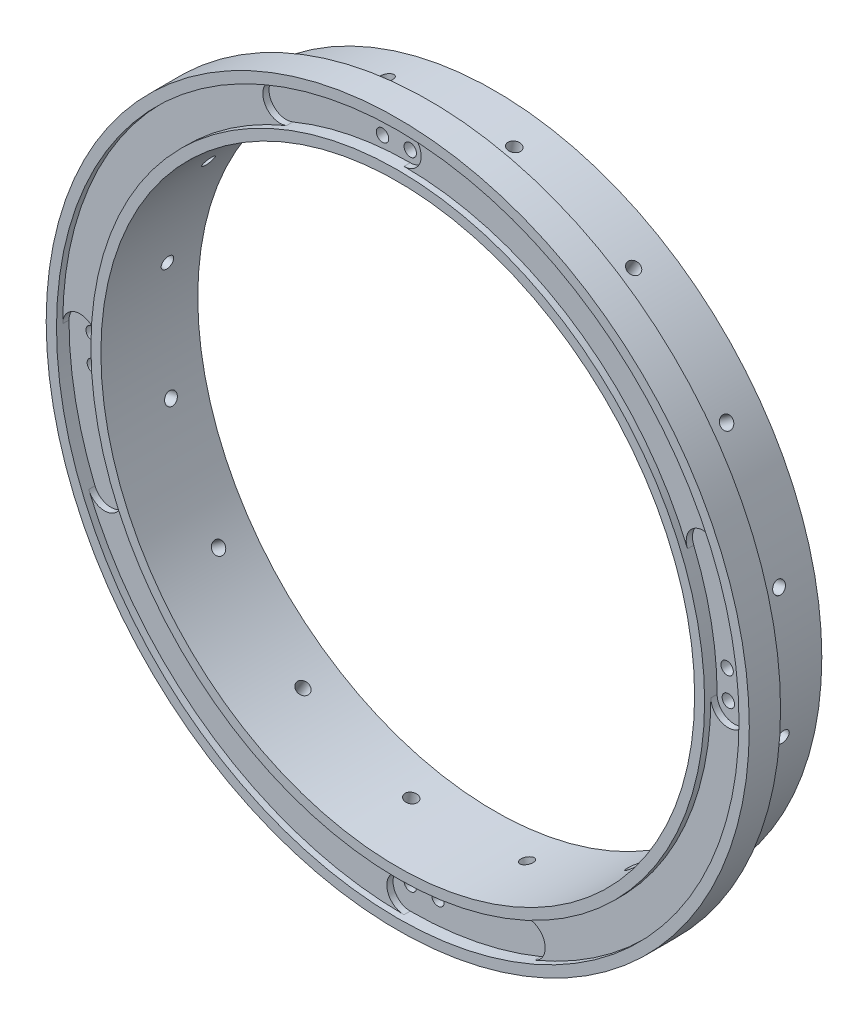
SolidWorks part; units mm, degrees
ref_plane "Front Plane" through (0, 0, 0) normal (0, 0, 1) x (1, 0, 0)
ref_plane "Top Plane" through (0, 0, 0) normal (0, 1, 0) x (1, 0, 0)
ref_plane "Right Plane" through (0, 0, 0) normal (1, 0, 0) x (0, 0, -1)
sketch "Sketch1" plane through (0, 0, 0) normal (0, 0, 1) x (1, 0, 0)
  circle A0 centre (0, 0) radius 71.4375
  dimension "D1" = 142.875
extrude "Extrude1" add sketch "Sketch1" along normal blind 19.685
sketch "Sketch2" plane through (0, 0, 19.685) normal (0, 0, 1) x (1, 0, 0)
  circle A0 centre (0, 0) radius 60.325
  dimension "D1" = 120.65
extrude "Extrude2" cut sketch "Sketch2" against normal through all
sketch "Sketch3" plane through (0, 0, 0) normal (0, 0, -1) x (-1, 0, 0)
  circle A0 centre (0, 0) radius 66.4845
  dimension "D1" = 132.969
extrude "Extrude3" cut sketch "Sketch3" against normal blind 13.335 flip side to cut
sketch "Sketch4" plane through (0, 0, 19.685) normal (0, 0, 1) x (1, 0, 0)
  circle A0 centre (0, 0) radius 62.357
  circle A1 centre (0, 0) radius 69.342
  dimension "D1" = 124.714
  dimension "D2" = 138.684
extrude "Extrude4" cut sketch "Sketch4" against normal blind 1.27
sketch "Sketch5" plane through (0, 0, 18.415) normal (0, 0, 1) x (1, 0, 0)
  line L0 (0, 0) -> (0, 69.342) construction
  line L1 (0, 69.342) -> (0, -69.342) construction
  line L2 (0, 0) -> (62.357, 0) construction
  line L3 (0, -69.342) -> (0, 0) construction
  line L4 (0, 0) -> (69.342, 0) construction
  line L5 (69.342, 0) -> (-69.342, 0) construction
  circle A0 centre (0, 0) radius 62.357 construction
  circle A2 centre (0, 0) radius 69.342 construction
sketch "Sketch7" plane through (0, 0, 18.415) normal (0, 0, 1) x (1, 0, 0)
  line L0 (69.342, 0) -> (-69.342, 0) construction
  line L1 (0, 0) -> (0, 69.342) construction
  line L2 (0, 69.342) -> (0, 62.357) construction
  line L3 (-26.536, 64.0637) -> (-23.863, 57.6104) construction
  arc A0 (0, 69.342) -> (-26.536, 64.0637) centre (0, 0) ccw
  arc A1 (0, 62.357) -> (-23.863, 57.6104) centre (0, 0) ccw
  circle A2 centre (0, 0) radius 62.357 construction
  arc A3 (-26.536, 64.0637) -> (-23.863, 57.6104) centre (-25.1995, 60.837) ccw
  arc A4 (0, 69.342) -> (0, 62.357) centre (0, 65.8495) cw
extrude "Extrude6" cut sketch "Sketch7" against normal blind 1.27 and the other way through all
pattern_circular "CirPattern1" count 4 over 360 about axis through (0, 0, 0) along (0, 0, 1) of "Extrude6"
sketch "Sketch8" plane through (0, 0, 17.145) normal (0, 0, 1) x (1, 0, 0)
  circle A0 centre (0, 0) radius 64.6327
  arc A1 (0, 64.6327) -> (-5.6331, 64.3868) centre (0, 0) ccw
hole_wizard "#39 (0.0995) Diameter Hole1" positions "3DSketch1" profile "Sketch9" hole size "#39" standard "Ansi Inch" end condition through all
sketch3d "3DSketch1"
  point P0 (0, 64.6327, 17.145)
  point P3 (-5.6331, 64.3868, 17.145)
sketch "Sketch9" plane through (0, 64.6327, 17.145) normal (1, 0, 0) x (0, -1, 0)
  line L0 (0, 0) -> (0, 17.145)
  line L1 (0, 17.145) -> (1.2636, 17.145)
  line L2 (1.2636, 17.145) -> (1.2636, 0)
  line L5 (1.2636, 0) -> (0, 0)
  line L11 (0, -6.35) -> (0, 107.95) construction
  dimension "Thru Hole Dia." = 2.5273
  dimension "Thru Hole Depth" = 17.145
pattern_circular "CirPattern2" count 4 over 360 about axis through (0, 0, 0) along (0, 0, 1) of "#39 (0.0995) Diameter Hole1"
ref_plane "Plane1" through (0, 0, 6.985) normal (0, 0, -1) x (-1, 0, 0)
sketch "Sketch15" plane through (0, 0, 6.985) normal (0, 0, -1) x (-1, 0, 0)
  line L0 (0, 0) -> (-66.4845, 0) construction
  line L1 (-2.314, 46.2834) -> (-2.314, 63.5529) construction
  line L2 (0, 0) -> (-69.342, 0) construction
  line L3 (0, 0) -> (-64.7805, 14.9558) construction
  circle A0 centre (0, 0) radius 66.4845 construction
ref_plane "Plane3" through (64.7805, 14.9558, 6.985) normal (0.9744, 0.225, 0) x (0, 0, -1)
hole_wizard "#39 (0.0995) Diameter Hole5" positions "Sketch17" profile "Sketch16" hole size "#39" standard "Ansi Inch"
sketch "Sketch17" plane through (64.7805, 14.9558, 6.985) normal (0.9744, 0.225, 0) x (0, 0, -1)
  point P1 (0, 0)
sketch "Sketch16" plane through (64.7805, 14.9558, 6.985) normal (0, 0, 1) x (-0.225, 0.9744, 0)
  line L0 (0, 0) -> (0, 13.4593)
  line L1 (0, 13.4593) -> (1.2636, 12.7)
  line L2 (1.2636, 12.7) -> (1.2636, 0)
  line L5 (1.2636, 0) -> (0, 0)
  line L10 (0, 13.4593) -> (-1.2636, 12.7) construction
  line L11 (0, -6.35) -> (0, 107.95) construction
  dimension "Hole Dia." = 2.5273
  dimension "Hole Depth" = 12.7
  dimension "Drill Angle" = 118
pattern_circular "CirPattern4" count 16 over 360 about axis through (0, 0, 0) along (0, 0, 1) of "#39 (0.0995) Diameter Hole5"
